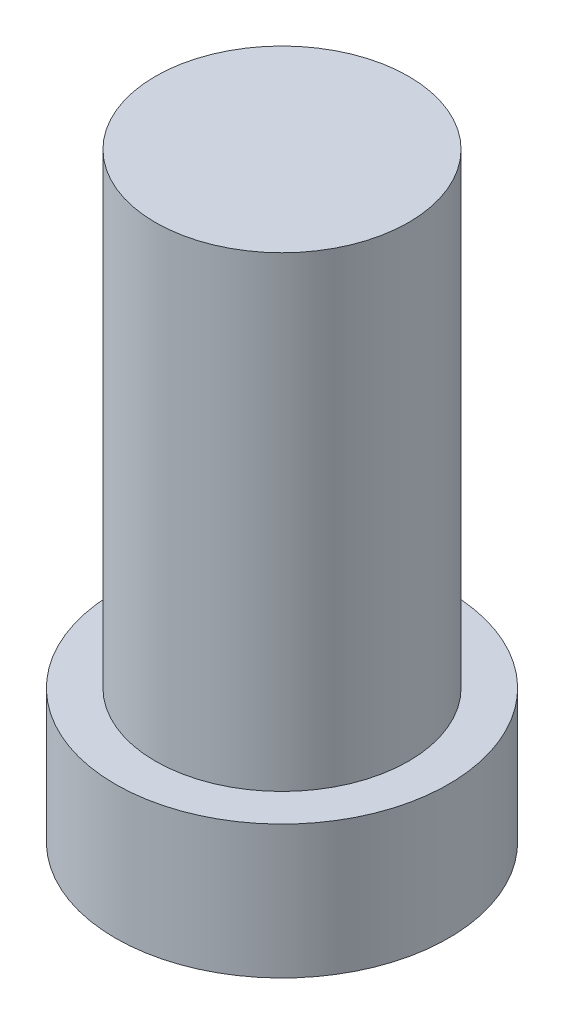
SolidWorks part; units mm, degrees
ref_plane "前视基准面" through (0, 0, 0) normal (0, 0, 1) x (1, 0, 0)
ref_plane "上视基准面" through (0, 0, 0) normal (0, 1, 0) x (1, 0, 0)
ref_plane "右视基准面" through (0, 0, 0) normal (1, 0, 0) x (0, 0, -1)
sketch "草图1" plane through (0, 0, 0) normal (0, 1, 0) x (1, 0, 0)
  circle A0 centre (0, 0) radius 5
  dimension "D1" = 10
extrude "凸台-拉伸1" add sketch "草图1" along normal blind 4
sketch "草图2" plane through (0, 4, 0) normal (0, 1, 0) x (1, 0, 0)
  circle A0 centre (0, 0) radius 3.8
  dimension "D1" = 7.6
extrude "凸台-拉伸2" add sketch "草图2" along normal blind 14
sketch "草图3" plane through (0, 0, 0) normal (0, -1, 0) x (1, 0, 0)
  circle A0 centre (0, 0) radius 3.5
  circle A1 centre (0, 0) radius 0.75
  circle A2 centre (0, 0) radius 5 construction
  dimension "D1" = 1.5
  dimension "D2" = 1.5
extrude "切除-拉伸1" cut sketch "草图3" against normal blind 3
